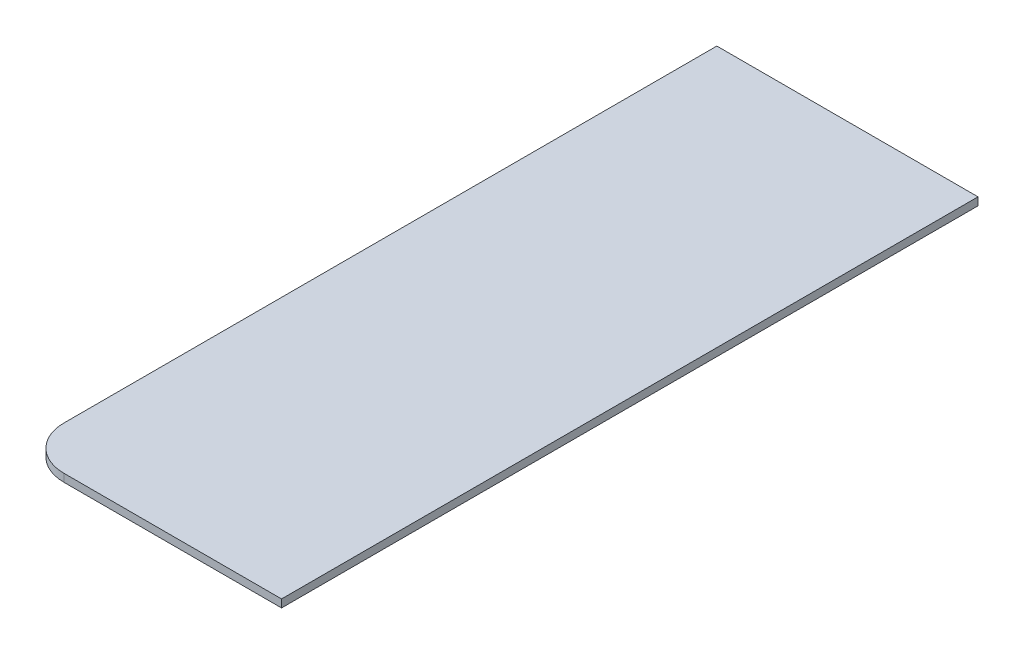
SolidWorks part; units mm, degrees
ref_plane "Спереди" through (0, 0, 0) normal (0, 0, 1) x (1, 0, 0)
ref_plane "Сверху" through (0, 0, 0) normal (0, 1, 0) x (1, 0, 0)
ref_plane "Справа" through (0, 0, 0) normal (1, 0, 0) x (0, 0, -1)
sketch "Эскиз1" plane through (0, 0, 0) normal (0, 1, 0) x (1, 0, 0)
  line L2 (938.2444, 115.6883) -> (938.2444, -1484.3117)
  line L5 (938.2444, 115.6883) -> (1538.2444, 115.6883)
  line L7 (938.2444, -1484.3117) -> (1538.2444, -1484.3117)
  line L8 (1538.2444, 115.6883) -> (1538.2444, -1484.3117)
  dimension "D3" = 600
  dimension "D4" = 1600
extrude "Бобышка-Вытянуть1" add sketch "Эскиз1" along normal blind 18
fillet "Fillet1" radius 100 1 edges at (938.2444, 9, 1484.3117)
